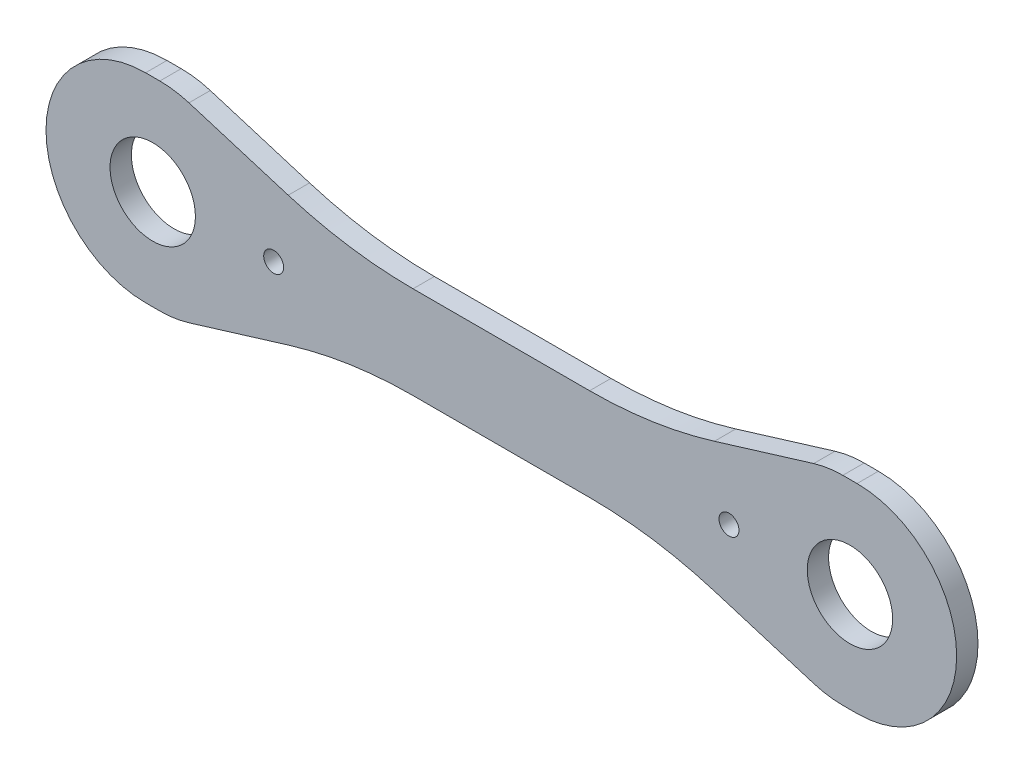
SolidWorks part; units mm, degrees
ref_plane "Plane1" through (0, 0, 0) normal (0, 0, 1) x (1, 0, 0)
ref_plane "Plane2" through (0, 0, 0) normal (0, 1, 0) x (1, 0, 0)
ref_plane "Plane3" through (0, 0, 0) normal (1, 0, 0) x (0, 0, -1)
sketch "Sketch1" plane through (0, 0, 0) normal (0, 0, 1) x (1, 0, 0)
  line L0 (0, 0) -> (0, 32.5) construction
  line L1 (0, 0) -> (-245, 0) construction
  line L2 (-250, 70) -> (-240, 70)
  line L3 (-219.534, 66.9413) -> (-149.7577, 45.6086)
  line L4 (-62.0462, 32.5) -> (62.0462, 32.5)
  line L5 (-62.0462, -32.5) -> (62.0462, -32.5)
  line L6 (-219.534, -66.9413) -> (-149.7577, -45.6086)
  line L7 (-250, -70) -> (-240, -70)
  line L8 (250, -70) -> (240, -70)
  line L9 (219.534, -66.9413) -> (149.7577, -45.6086)
  line L10 (219.534, 66.9413) -> (149.7577, 45.6086)
  line L11 (250, 70) -> (240, 70)
  circle A0 centre (-245, 0) radius 30 construction
  arc A1 (-250, 70) -> (-250, -70) centre (-250, 0) ccw
  arc A2 (-240, 70) -> (-219.534, 66.9413) centre (-240, 0) cw
  arc A3 (-149.7577, 45.6086) -> (-62.0462, 32.5) centre (-62.0462, 332.5) ccw
  arc A4 (-149.7577, -45.6086) -> (-62.0462, -32.5) centre (-62.0462, -332.5) cw
  arc A5 (-240, -70) -> (-219.534, -66.9413) centre (-240, 0) ccw
  arc A6 (240, -70) -> (219.534, -66.9413) centre (240, 0) cw
  arc A7 (149.7577, -45.6086) -> (62.0462, -32.5) centre (62.0462, -332.5) ccw
  arc A8 (149.7577, 45.6086) -> (62.0462, 32.5) centre (62.0462, 332.5) cw
  arc A9 (240, 70) -> (219.534, 66.9413) centre (240, 0) ccw
  arc A10 (250, 70) -> (250, -70) centre (250, 0) cw
  circle A11 centre (245, 0) radius 30 construction
  circle A12 centre (-160, 0) radius 7 construction
  circle A13 centre (160, 0) radius 7 construction
  dimension "D1" = 60
  dimension "D4" = 70
  dimension "D7" = 300
  dimension "D10" = 14
  dimension "D2" = 5
  dimension "D3" = 5
  dimension "D5" = 65
  dimension "D6" = 17
  dimension "D8" = 490
  dimension "D9" = 85
extrude "Extrude1" add sketch "Sketch1" along normal blind 15
cosmetic thread "Cosmetic Thread1" parameters "D2"=16
sketch "Sketch2" plane through (0, 0, 15) normal (0, 0, 1) x (1, 0, 0)
  circle A0 centre (245, 0) radius 30 construction
  circle A1 centre (-245, 0) radius 30 construction
  circle A2 centre (245, 0) radius 30
  circle A3 centre (-245, 0) radius 30
extrude "ø60 udboringer" cut sketch "Sketch2" against normal through all
sketch "Sketch3" plane through (0, 0, 15) normal (0, 0, 1) x (1, 0, 0)
  circle A0 centre (160, 0) radius 7 construction
  circle A1 centre (-160, 0) radius 7 construction
  circle A2 centre (160, 0) radius 7
  circle A3 centre (-160, 0) radius 7
extrude "M16 gevindhuller" cut sketch "Sketch3" against normal through all
cosmetic thread "Cosmetic Thread2" parameters "D2"=16
cosmetic thread "Cosmetic Thread3" parameters "D2"=16
